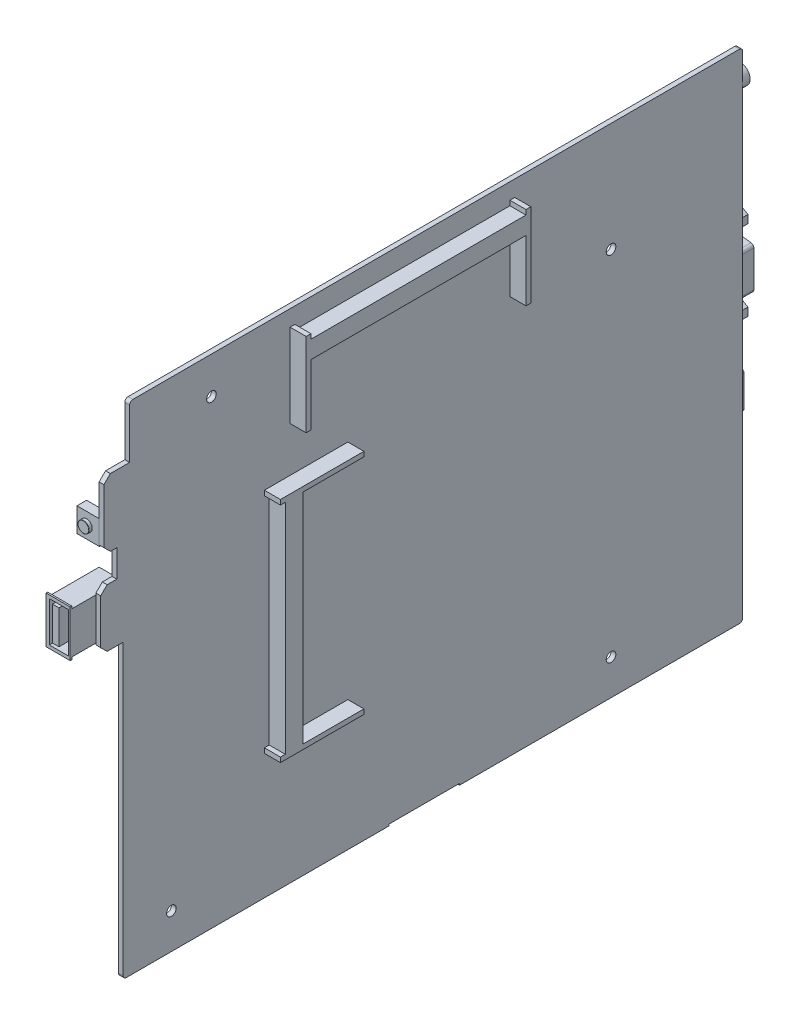
SolidWorks part; units mm, degrees
ref_plane "前视基准面" through (0, 0, 0) normal (0, 0, 1) x (1, 0, 0)
ref_plane "上视基准面" through (0, 0, 0) normal (0, 1, 0) x (1, 0, 0)
ref_plane "右视基准面" through (0, 0, 0) normal (1, 0, 0) x (0, 0, -1)
sketch "草图1" plane through (0, 0, 0) normal (1, 0, 0) x (0, 0, -1)
  line L0 (0, 0) -> (0, 46.6833) construction
  line L1 (-94.5, 77.5) -> (96.5, 77.5)
  line L2 (-96.5, 13.5) -> (-96.5, -77.5)
  line L3 (-96.5, -77.5) -> (96.5, -77.5)
  line L4 (96.5, 77.5) -> (96.5, -77.5)
  line L5 (-94.5, 75.8938) -> (96.5, -77.5) construction
  line L6 (-96.5, -77.5) -> (96.5, 77.5) construction
  line L11 (0, 0) -> (-41.6392, 0) construction
  line L18 (-94.5, 77.5) -> (-94.5, 61)
  line L19 (-94.5, 61) -> (-102.5, 61)
  line L20 (-96.5, 13.5) -> (-103.5, 13.5)
  line L21 (-103.5, 13.5) -> (-103.5, 31.5)
  line L22 (-103.5, 31.5) -> (-98.5, 31.5)
  line L23 (-98.5, 31.5) -> (-98.5, 40)
  line L24 (-98.5, 40) -> (-102.5, 40)
  line L25 (-102.5, 40) -> (-102.5, 61)
  point P0 (0, 0)
  point P21 (-98.5, 35.75)
  dimension "D1" = 193
  dimension "D2" = 155
  dimension "D3" = 8.5
  dimension "D11" = 191
  dimension "D12" = 16.5
  dimension "D13" = 5
  dimension "D14" = 200
  dimension "D15" = 199
  dimension "D16" = 18
  dimension "D17" = 21
extrude "凸台-拉伸1" add sketch "草图1" against normal blind 1.5
chamfer "倒角1" distance 2 angle 45 4 edges at (-0.75, 13.5, 103.5) (-0.75, 31.5, 103.5) (-0.75, 40, 102.5) (-0.75, 61, 102.5)
fillet "圆角1" radius 1 4 edges at (-0.75, 77.5, -96.5) (-0.75, -77.5, -96.5) (-0.75, -77.5, 96.5) (-0.75, 77.5, 94.5)
sketch "草图2" plane through (0, 0, 0) normal (1, 0, 0) x (0, 0, -1)
  line L0 (95.5, 77.5) -> (-93.5, 77.5) construction
  line L1 (-44.5, 72.5) -> (25.5, 72.5)
  line L2 (-44.5, 72.5) -> (-44.5, 35.5)
  line L3 (-44.5, 35.5) -> (25.5, 35.5)
  line L4 (25.5, 72.5) -> (25.5, 35.5)
  line L5 (-52.5, 32.5) -> (-15.5, 32.5)
  line L6 (-52.5, 32.5) -> (-52.5, -38.5)
  line L7 (-52.5, -38.5) -> (-15.5, -38.5)
  line L8 (-15.5, 32.5) -> (-15.5, -38.5)
  line L9 (96.5, -76.5) -> (96.5, 76.5) construction
  line L11 (-85.5, -3.5) -> (-54.5, -3.5)
  line L12 (-85.5, -3.5) -> (-85.5, -60.5)
  line L13 (-85.5, -60.5) -> (-54.5, -60.5)
  line L14 (-54.5, -3.5) -> (-54.5, -60.5)
  dimension "D1" = 70
  dimension "D2" = 71
  dimension "D3" = 37
  dimension "D4" = 37
  dimension "D5" = 45
  dimension "D6" = 5
  dimension "D7" = 71
  dimension "D8" = 112
  dimension "D9" = 31
  dimension "D10" = 57
  dimension "D11" = 2
  dimension "D12" = 81
sketch "草图3" plane through (0, 0, 0) normal (1, 0, 0) x (0, 0, -1)
  line L0 (-44.5, 46.5) -> (-43, 46.5)
  line L1 (-44.5, 72.5) -> (-44.5, 35.5) construction
  line L2 (-43, 46.5) -> (-43, 65.5)
  line L3 (-43, 65.5) -> (24, 65.5)
  line L4 (24, 65.5) -> (24, 46.5)
  line L5 (24, 46.5) -> (25.5, 46.5)
  line L6 (25.5, 72.5) -> (25.5, 35.5) construction
  line L7 (25.5, 46.5) -> (25.5, 72.5)
  line L8 (25.5, 72.5) -> (24, 72.5)
  line L9 (-44.5, 72.5) -> (-44.5, 46.5)
  line L10 (-43, 72.5) -> (-44.5, 72.5)
  line L12 (-43, 72.5) -> (-43, 71)
  line L13 (-43, 71) -> (24, 71)
  line L14 (24, 72.5) -> (24, 71)
  line L15 (-52.5, -38.5) -> (-15.5, -38.5) construction
  line L16 (-52.5, 32.5) -> (-26.5, 32.5)
  line L17 (-52.5, 32.5) -> (-52.5, 31)
  line L18 (-52.5, -38.5) -> (-26.5, -38.5)
  line L19 (-26.5, 32.5) -> (-26.5, 31)
  line L20 (-52.5, -37) -> (-52.5, -38.5)
  line L21 (-26.5, -37) -> (-45.5, -37)
  line L23 (-26.5, 31) -> (-45.5, 31)
  line L24 (-45.5, -37) -> (-45.5, 31)
  line L25 (-52.5, 31) -> (-51, 31)
  line L27 (-52.5, -37) -> (-51, -37)
  line L28 (-51, 31) -> (-51, -37)
  line L29 (-26.5, -37) -> (-26.5, -38.5)
  dimension "D1" = 1.5
  dimension "D2" = 7
  dimension "D3" = 5.5
  dimension "D4" = 26
  dimension "D5" = 5.5
  dimension "D6" = 7
extrude "凸台-拉伸2" add sketch "草图3" along normal blind 5
sketch "草图4" plane through (-1.5, 0, 0) normal (-1, 0, 0) x (0, 0, 1)
  line L0 (95.5, -77.5) -> (-95.5, -77.5) construction
  line L1 (-9.75, -70) -> (15.25, -70)
  line L2 (-9.75, -70) -> (-9.75, -78.5)
  line L3 (-9.75, -78.5) -> (15.25, -78.5)
  line L4 (15.25, -70) -> (15.25, -78.5)
  line L6 (-96.5, -76.5) -> (-96.5, 76.5) construction
  dimension "D1" = 8.5
  dimension "D2" = 25
  dimension "D3" = 7.5
  dimension "D4" = 111.75
extrude "凸台-拉伸3" add sketch "草图4" along normal blind 11
sketch "草图5" plane through (-12.5, 0, 0) normal (-1, 0, 0) x (0, 0, 1)
  line L0 (-9.75, -70) -> (-9.75, -78.5) construction
  line L1 (-8.25, -72.5) -> (3.25, -72.5)
  line L2 (-8.25, -72.5) -> (-8.25, -74.5)
  line L3 (-8.25, -74.5) -> (3.25, -74.5)
  line L4 (3.25, -72.5) -> (3.25, -74.5)
  line L5 (4.75, -72.5) -> (13.75, -72.5)
  line L6 (4.75, -72.5) -> (4.75, -74.5)
  line L7 (4.75, -74.5) -> (13.75, -74.5)
  line L8 (13.75, -72.5) -> (13.75, -74.5)
  line L9 (-9.75, -72.5) -> (-9.25, -72.5)
  line L10 (-9.75, -72.5) -> (-9.75, -74.5)
  line L11 (-9.75, -74.5) -> (-9.25, -74.5)
  line L12 (-9.25, -72.5) -> (-9.25, -74.5)
  line L13 (15.25, -78.5) -> (15.25, -70) construction
  line L14 (15.25, -72.5) -> (14.75, -72.5)
  line L15 (15.25, -72.5) -> (15.25, -74.5)
  line L16 (15.25, -74.5) -> (14.75, -74.5)
  line L17 (14.75, -72.5) -> (14.75, -74.5)
  line L18 (15.25, -70) -> (-9.75, -70) construction
  dimension "D1" = 0.5
  dimension "D2" = 2.5
  dimension "D3" = 2
  dimension "D4" = 1
  dimension "D5" = 1.5
  dimension "D6" = 1
  dimension "D7" = 11.5
extrude "切除-拉伸1" cut sketch "草图5" against normal blind 8
sketch "草图6" plane through (-12.5, 0, 0) normal (-1, 0, 0) x (0, 0, 1)
  line L0 (-9.75, -78.5) -> (15.25, -78.5) construction
  line L1 (-8.25, -78.5) -> (13.75, -78.5)
  line L2 (-8.25, -78.5) -> (-8.25, -77)
  line L3 (-8.25, -77) -> (13.75, -77)
  line L4 (13.75, -78.5) -> (13.75, -77)
  line L5 (4.75, -74.5) -> (13.75, -74.5) construction
  line L6 (-8.25, -72.5) -> (-8.25, -74.5) construction
  line L7 (13.75, -74.5) -> (13.75, -72.5) construction
  dimension "D1" = 2.5
extrude "切除-拉伸2" cut sketch "草图6" against normal through all
sketch "草图7" plane through (-1.5, 0, 0) normal (-1, 0, 0) x (0, 0, 1)
  line L0 (103.5, 22.5) -> (89.2944, 22.5) construction
  line L1 (111, 29.75) -> (111.5, 29.75)
  line L2 (95.5, 29) -> (95.5, 16)
  line L3 (111, 15.25) -> (111.5, 15.25)
  line L4 (111.5, 29.75) -> (111.5, 15.25)
  line L6 (103.5, 29.5) -> (103.5, 15.5) construction
  line L10 (95.5, 29) -> (111, 29)
  line L11 (111, 29.75) -> (111, 29)
  line L14 (95.5, 16) -> (111, 16)
  line L15 (111, 15.25) -> (111, 16)
  dimension "D1" = 0.5
  dimension "D2" = 14.5
  dimension "D3" = 16
  dimension "D4" = 8
  dimension "D5" = 13
extrude "凸台-拉伸4" add sketch "草图7" along normal blind 7.5
sketch "草图8" plane through (-9, 0, 0) normal (-1, 0, 0) x (0, 0, 1)
  line L1 (95.5, 29) -> (111, 29)
  line L2 (95.5, 29) -> (95.5, 16)
  line L3 (95.5, 16) -> (111, 16)
  line L4 (111, 29) -> (111, 16)
extrude "切除-拉伸3" cut sketch "草图8" against normal blind 0.5
sketch "草图9" plane through (0, 0, 111.5) normal (0, 0, 1) x (1, 0, 0)
  line L0 (-9, 29.75) -> (-1.5, 29.75) construction
  line L1 (-8, 28.75) -> (-2, 28.75)
  line L2 (-8, 28.75) -> (-8, 16.25)
  line L3 (-8, 16.25) -> (-2, 16.25)
  line L4 (-2, 28.75) -> (-2, 16.25)
  line L5 (-7, 27.75) -> (-5, 27.75)
  line L6 (-7, 27.75) -> (-7, 17.25)
  line L7 (-7, 17.25) -> (-5, 17.25)
  line L8 (-5, 27.75) -> (-5, 17.25)
  line L9 (-9, 15.25) -> (-9, 29.75) construction
  line L10 (-9, 15.25) -> (-1.5, 15.25) construction
  line L11 (-1.5, 29) -> (-1.5, 16) construction
  dimension "D1" = 1
  dimension "D2" = 1
  dimension "D3" = 1
  dimension "D4" = 0.5
  dimension "D5" = 1
  dimension "D6" = 2
  dimension "D7" = 1
  dimension "D8" = 1
extrude "切除-拉伸4" cut sketch "草图9" against normal blind 13
sketch "草图10" plane through (-1.5, 0, 0) normal (-1, 0, 0) x (0, 0, 1)
  line L0 (102.5, 59) -> (102.5, 42) construction
  line L1 (102.4, 49) -> (99.4, 49)
  line L3 (102.4, 41.5) -> (99.4, 41.5)
  line L4 (99.4, 49) -> (99.4, 41.5)
  line L5 (94.5, 61) -> (100.5, 61) construction
  line L6 (102.4, 49) -> (102.4, 41.5)
  dimension "D1" = 12
  dimension "D2" = 7.5
  dimension "D3" = 3
  dimension "D4" = 0.1
extrude "凸台-拉伸5" add sketch "草图10" along normal blind 7
sketch "草图11" plane through (0, 0, 102.4) normal (0, 0, 1) x (1, 0, 0)
  line L0 (-8.5, 45.25) -> (1.2672, 45.25) construction
  line L1 (-8.5, 41.5) -> (-8.5, 49) construction
  circle A0 centre (-5.5, 45.25) radius 1.75
  dimension "D1" = 3.5
  dimension "D2" = 3
extrude "凸台-拉伸6" add sketch "草图11" along normal blind 1
fillet "圆角2" radius 0.1 1 edges at (-3.75, 45.25, 103.4)
sketch "草图12" plane through (-1.5, 0, 0) normal (-1, 0, 0) x (0, 0, 1)
  line L0 (-96.5, -76.5) -> (-96.5, 76.5) construction
  line L1 (-96.6, 72.5) -> (-81.6, 72.5)
  line L2 (-96.6, 72.5) -> (-96.6, 62.5)
  line L3 (-96.6, 62.5) -> (-81.6, 62.5)
  line L4 (-81.6, 72.5) -> (-81.6, 62.5)
  line L5 (-95.5, 77.5) -> (93.5, 77.5) construction
  dimension "D1" = 0.1
  dimension "D2" = 5
  dimension "D3" = 15
  dimension "D4" = 10
extrude "凸台-拉伸7" add sketch "草图12" along normal blind 4.5
sketch "草图13" plane through (0, 0, -96.6) normal (0, 0, -1) x (-1, 0, 0)
  line L0 (6, 67.5) -> (9.0348, 67.5) construction
  line L1 (6, 72.5) -> (6, 62.5) construction
  line L5 (0, -76.5) -> (0, 76.5) construction
  circle A0 centre (3.25, 67.5) radius 3
  circle A1 centre (3.25, 67.5) radius 1.5
  point P9 (0, 0)
  dimension "D1" = 6
  dimension "D2" = 3
  dimension "D3" = 3.25
extrude "凸台-拉伸8" add sketch "草图13" along normal blind 2.5
sketch "草图14" plane through (-1.5, 0, 0) normal (-1, 0, 0) x (0, 0, 1)
  line L0 (-96.5, -76.5) -> (-96.5, 62.5) construction
  line L1 (-96.4, 60.5) -> (-93.9, 60.5)
  line L2 (-96.4, 60.5) -> (-96.4, 53.5)
  line L3 (-96.4, 53.5) -> (-93.9, 53.5)
  line L4 (-93.9, 60.5) -> (-93.9, 53.5)
  line L5 (-96.4, 50.5) -> (-93.9, 50.5)
  line L6 (-96.4, 50.5) -> (-96.4, 43.5)
  line L7 (-96.4, 43.5) -> (-93.9, 43.5)
  line L8 (-93.9, 50.5) -> (-93.9, 43.5)
  line L9 (-96.5, 62.5) -> (-81.6, 62.5) construction
  dimension "D1" = 0.1
  dimension "D2" = 7
  dimension "D3" = 2.5
  dimension "D4" = 2
  dimension "D5" = 3
extrude "凸台-拉伸9" add sketch "草图14" along normal blind 3.5
sketch "草图15" plane through (0, 0, -96.4) normal (0, 0, -1) x (-1, 0, 0)
  line L0 (5, 57) -> (1.1058, 57) construction
  line L1 (2.5, 58.5) -> (4, 58.5)
  line L2 (2.5, 58.5) -> (2.5, 55.5)
  line L3 (2.5, 55.5) -> (4, 55.5)
  line L4 (4, 58.5) -> (4, 55.5)
  line L5 (5, 60.5) -> (5, 53.5) construction
  line L6 (3.25, 60.5) -> (3.25, 53.0774) construction
  line L7 (5, 60.5) -> (1.5, 60.5) construction
  line L8 (5, 47) -> (-0.6417, 47) construction
  line L9 (5, 50.5) -> (5, 43.5) construction
  line L11 (2.5, 48.5) -> (4, 48.5)
  line L12 (2.5, 48.5) -> (2.5, 45.5)
  line L13 (2.5, 45.5) -> (4, 45.5)
  line L14 (4, 48.5) -> (4, 45.5)
  dimension "D1" = 1.5
  dimension "D2" = 3
extrude "凸台-拉伸10" add sketch "草图15" along normal blind 1
sketch "草图16" plane through (-1.5, 0, 0) normal (-1, 0, 0) x (0, 0, 1)
  line L0 (-96.5, -76.5) -> (-96.5, 62.5) construction
  line L1 (-95.5, 41.5) -> (-92.5, 41.5)
  line L2 (-95.5, 41.5) -> (-95.5, 32.5)
  line L3 (-95.5, 32.5) -> (-92.5, 32.5)
  line L4 (-92.5, 41.5) -> (-92.5, 32.5)
  line L5 (-96.4, 43.5) -> (-93.9, 43.5) construction
  dimension "D1" = 1
  dimension "D2" = 9
  dimension "D3" = 3
  dimension "D4" = 2
extrude "凸台-拉伸11" add sketch "草图16" along normal blind 2.5
sketch "草图17" plane through (0, 0, -95.5) normal (0, 0, -1) x (-1, 0, 0)
  line L0 (4, 41.5) -> (4, 32.5) construction
  line L1 (2.5, 40) -> (3, 40)
  line L2 (2.5, 40) -> (2.5, 38.5)
  line L3 (2.5, 38.5) -> (3, 38.5)
  line L4 (3, 40) -> (3, 38.5)
  line L5 (4, 41.5) -> (1.5, 41.5) construction
  dimension "D1" = 0.5
  dimension "D2" = 1.5
  dimension "D3" = 1
  dimension "D4" = 1.5
extrude "凸台-拉伸12" add sketch "草图17" along normal blind 2
sketch "草图18" plane through (-1.5, 0, 0) normal (-1, 0, 0) x (0, 0, 1)
  line L0 (-96.5, -76.5) -> (-96.5, 62.5) construction
  line L1 (-97.5, 28) -> (-93, 28)
  line L2 (-97.5, 28) -> (-97.5, -3)
  line L3 (-97.5, -3) -> (-93, -3)
  line L4 (-93, 28) -> (-93, -3)
  line L5 (-95.5, 32.5) -> (-92.5, 32.5) construction
  point P6 (-95.25, 28)
  dimension "D1" = 1
  dimension "D2" = 4.5
  dimension "D3" = 4.5
  dimension "D4" = 31
extrude "凸台-拉伸13" add sketch "草图18" along normal blind 12
sketch "草图19" plane through (0, 0, -97.5) normal (0, 0, -1) x (-1, 0, 0)
  line L0 (7.5, 28) -> (7.5, 8.154) construction
  line L1 (7.5, 22.5) -> (9.6651, 23.75)
  line L2 (9.6651, 23.75) -> (9.6651, 26.25)
  line L3 (9.6651, 26.25) -> (7.5, 27.5)
  line L4 (7.5, 27.5) -> (5.3349, 26.25)
  line L5 (5.3349, 26.25) -> (5.3349, 23.75)
  line L6 (5.3349, 23.75) -> (7.5, 22.5)
  line L7 (7.5, -2.5) -> (9.6651, -1.25)
  line L8 (9.6651, -1.25) -> (9.6651, 1.25)
  line L9 (9.6651, 1.25) -> (7.5, 2.5)
  line L10 (7.5, 2.5) -> (5.3349, 1.25)
  line L11 (5.3349, 1.25) -> (5.3349, -1.25)
  line L12 (5.3349, -1.25) -> (7.5, -2.5)
  line L13 (13.5, 28) -> (1.5, 28) construction
  line L14 (13.5, 12.5) -> (1.5, 12.5) construction
  line L15 (13.5, 28) -> (13.5, -3) construction
  line L16 (1.5, 28) -> (1.5, -3) construction
  circle A0 centre (7.5, 25) radius 2.1651 construction
  circle A1 centre (7.5, 0) radius 2.1651 construction
  dimension "D1" = 2.5
  dimension "D2" = 25
extrude "凸台-拉伸14" add sketch "草图19" along normal blind 6
sketch "草图20" plane through (0, 0, -97.5) normal (0, 0, -1) x (-1, 0, 0)
  line L0 (3.5, 18.1172) -> (3.5, 6.8828)
  line L1 (4.376, 5.8905) -> (10.376, 5.1405)
  line L2 (11.5, 6.1328) -> (11.5, 18.8672)
  line L3 (10.376, 19.8595) -> (4.376, 19.1095)
  line L4 (13.5, 12.5) -> (-2.3142, 12.5) construction
  line L5 (13.5, 28) -> (13.5, -3) construction
  line L6 (7.5, 28) -> (7.5, -3) construction
  line L7 (13.5, 28) -> (1.5, 28) construction
  line L8 (13.5, -3) -> (1.5, -3) construction
  arc A0 (4.376, 5.8905) -> (3.5, 6.8828) centre (4.5, 6.8828) cw
  arc A1 (3.5, 18.1172) -> (4.376, 19.1095) centre (4.5, 18.1172) cw
  arc A2 (10.376, 5.1405) -> (11.5, 6.1328) centre (10.5, 6.1328) ccw
  arc A3 (11.5, 18.8672) -> (10.376, 19.8595) centre (10.5, 18.8672) ccw
  point P16 (3.5, 6)
  point P19 (3.5, 19)
  point P22 (11.5, 5)
  point P25 (11.5, 20)
  dimension "D4" = 1
  dimension "D5" = 1
  dimension "D1" = 8
  dimension "D2" = 13
  dimension "D3" = 15
extrude "凸台-拉伸15" add sketch "草图20" along normal up to surface (6 mm away) up to face at (-7.5, 0, -103.5)
hole_wizard "M3 螺纹孔1" positions "草图21" profile "草图22" tap size "M3" standard "GB"
sketch "草图21" plane through (0, 0, -103.5) normal (0, 0, -1) x (-1, 0, 0)
  point P0 (7.5079, 25.0935)
  point P3 (7.5079, 0)
sketch "草图22" plane through (-7.5079, 25.0935, -103.5) normal (1, 0, 0) x (0, 1, 0)
  line L0 (0, 0) -> (0, 8.2511)
  line L1 (0, 8.2511) -> (1.25, 7.5)
  line L2 (1.25, 7.5) -> (1.25, 0.25)
  line L3 (1.25, 0.25) -> (1.5, 0)
  line L5 (1.5, 0) -> (0, 0)
  line L6 (-1.25, 0.25) -> (-1.5, 0) construction
  line L10 (0, 8.2511) -> (-1.25, 7.5) construction
  line L11 (0, -6.35) -> (0, 107.95) construction
  dimension "螺纹孔钻头直径" = 2.5
  dimension "螺纹孔钻头深度" = 7.5
  dimension "近端锥形沉头孔直径" = 3
  dimension "近端锥形沉头孔角度" = 90
  dimension "导头角度" = 118
cosmetic thread "孔螺蚊线1" parameters "D1"=6, "D2"=3
cosmetic thread "孔螺蚊线2" parameters "D1"=6, "D2"=3
sketch "草图23" plane through (0, 0, -103.5) normal (0, 0, -1) x (-1, 0, 0)
  line L0 (7.376, 19.4845) -> (7.376, 11.5981) construction
  line L1 (10.376, 19.8595) -> (4.376, 19.1095) construction
  line L2 (9.5, 17.5) -> (7.7703, 17.5) construction
  line L3 (11.5, 6.1328) -> (11.5, 18.8672) construction
  line L4 (3.5, 18.1172) -> (3.5, 6.8828) construction
  line L5 (11.5, 12.5) -> (3.5, 12.5) construction
  line L6 (11.5, 6.1328) -> (11.5, 18.8672) construction
  line L7 (3.5, 18.1172) -> (3.5, 6.8828) construction
  circle A0 centre (9.5, 17.5) radius 0.5
  circle A1 centre (7.376, 16.25) radius 0.5
  circle A2 centre (5.5, 17.5) radius 0.5
  dimension "D1" = 1
  dimension "D2" = 2
  dimension "D3" = 2
  dimension "D4" = 10
  dimension "D5" = 1.25
extrude "切除-拉伸5" cut sketch "草图23" against normal blind 5
pattern_linear "阵列(线性)1" count 5 spacing 2.5 along (0, -1, 0) of "切除-拉伸5"
sketch "草图24" plane through (-1.5, 0, 0) normal (-1, 0, 0) x (0, 0, 1)
  line L0 (-96.5, -76.5) -> (-96.5, -3) construction
  line L1 (-98.5, -9.5) -> (-86.5, -9.5)
  line L2 (-98.5, -9.5) -> (-98.5, -24.5)
  line L3 (-98.5, -24.5) -> (-86.5, -24.5)
  line L4 (-86.5, -9.5) -> (-86.5, -24.5)
  line L5 (-96.5, -3) -> (-93, -3) construction
  dimension "D1" = 2
  dimension "D2" = 6.5
  dimension "D3" = 12
  dimension "D4" = 15
extrude "凸台-拉伸16" add sketch "草图24" along normal blind 6
sketch "草图25" plane through (0, 0, -98.5) normal (0, 0, -1) x (-1, 0, 0)
  line L0 (7.5, -9.5) -> (1.5, -9.5) construction
  line L1 (1.5, -9.5) -> (3.5, -9.5)
  line L2 (3.5, -9.5) -> (1.5, -12)
  line L3 (1.5, -9.5) -> (1.5, -24.5) construction
  line L4 (1.5, -12) -> (1.5, -9.5)
  line L5 (1.5, -22) -> (3.5, -24.5)
  line L6 (1.5, -24.5) -> (1.5, -9.5) construction
  line L7 (7.5, -24.5) -> (1.5, -24.5) construction
  line L8 (3.5, -24.5) -> (1.5, -24.5)
  line L9 (1.5, -24.5) -> (1.5, -22)
  line L10 (7.5, -9.5) -> (7.5, -24.5) construction
  line L11 (7.5, -17) -> (1.5, -17) construction
  line L12 (7, -10) -> (3.7403, -10)
  line L13 (3.7403, -10) -> (2, -12.1754)
  line L14 (2, -12.1754) -> (2, -21.8246)
  line L15 (2, -21.8246) -> (3.7403, -24)
  line L16 (3.7403, -24) -> (7, -24)
  line L17 (7, -24) -> (7, -10)
  line L19 (4, -12) -> (5, -12)
  line L20 (4, -12) -> (4, -22)
  line L21 (4, -22) -> (5, -22)
  line L22 (5, -12) -> (5, -22)
  dimension "D1" = 4
  dimension "D2" = 10
  dimension "D3" = 0.5
  dimension "D4" = 0.5
  dimension "D5" = 0.5
  dimension "D6" = 0.5
  dimension "D7" = 0.5
  dimension "D8" = 0.5
  dimension "D9" = 1
  dimension "D10" = 2
  dimension "D11" = 2
extrude "切除-拉伸6" cut sketch "草图25" against normal blind 10
sketch "草图26" plane through (0, 0, -98.5) normal (0, 0, -1) x (-1, 0, 0)
  line L1 (4, -12) -> (5, -12)
  line L2 (4, -12) -> (4, -22)
  line L3 (4, -22) -> (5, -22)
  line L4 (5, -12) -> (5, -22)
extrude "切除-拉伸7" cut sketch "草图26" against normal blind 2
sketch "草图27" plane through (-1.5, 0, 0) normal (-1, 0, 0) x (0, 0, 1)
  line L0 (-96.5, -76.5) -> (-96.5, -22) construction
  line L1 (-98, -28) -> (-69.5, -28)
  line L2 (-98, -28) -> (-98, -45.5)
  line L3 (-98, -45.5) -> (-69.5, -45.5)
  line L4 (-69.5, -28) -> (-69.5, -45.5)
  line L5 (-98.5, -24.5) -> (-86.5, -24.5) construction
  dimension "D1" = 1.5
  dimension "D2" = 28.5
  dimension "D3" = 17.5
  dimension "D4" = 3.5
extrude "凸台-拉伸17" add sketch "草图27" along normal blind 26
sketch "草图28" plane through (0, 0, -98) normal (0, 0, -1) x (-1, 0, 0)
  line L0 (27.5, -36.75) -> (26, -36.75) construction
  line L1 (4.5, -30.75) -> (11.5, -30.75)
  line L2 (4.5, -30.75) -> (4.5, -33.75)
  line L3 (4.5, -42.75) -> (11.5, -42.75)
  line L4 (11.5, -30.75) -> (11.5, -42.75)
  line L5 (27.5, -28) -> (27.5, -45.5) construction
  line L6 (1.5, -45.5) -> (1.5, -28) construction
  line L7 (4.5, -39.75) -> (4.5, -42.75)
  line L8 (4.5, -33.75) -> (3, -33.75)
  line L10 (4.5, -39.75) -> (3, -39.75)
  line L11 (3, -33.75) -> (3, -39.75)
  line L12 (1.5, -28) -> (1.5, -45.5) construction
  line L13 (24.5, -39.75) -> (24.5, -42.75)
  line L14 (17.5, -30.75) -> (24.5, -30.75)
  line L15 (17.5, -30.75) -> (17.5, -42.75)
  line L16 (17.5, -42.75) -> (24.5, -42.75)
  line L17 (24.5, -30.75) -> (24.5, -33.75)
  line L18 (24.5, -33.75) -> (26, -33.75)
  line L20 (24.5, -39.75) -> (26, -39.75)
  line L21 (26, -33.75) -> (26, -39.75)
  line L22 (21.5667, -36.75) -> (1.5, -36.75) construction
  point P14 (4.5, -32.25)
  dimension "D1" = 6
  dimension "D2" = 12
  dimension "D3" = 7
  dimension "D4" = 1.5
  dimension "D5" = 1.5
  dimension "D6" = 1.5
extrude "切除-拉伸8" cut sketch "草图28" against normal blind 10
sketch "草图29" plane through (0, 0, -98) normal (0, 0, -1) x (-1, 0, 0)
  line L0 (26, -39.75) -> (26, -33.75) construction
  line L1 (26, -34.75) -> (27.5, -34.75)
  line L2 (26, -34.75) -> (26, -38.75)
  line L3 (26, -38.75) -> (27.5, -38.75)
  line L4 (27.5, -34.75) -> (27.5, -38.75)
  line L5 (27.5, -28) -> (27.5, -45.5) construction
  line L6 (1.5, -36.75) -> (29.6783, -36.75) construction
  line L7 (1.5, -45.5) -> (1.5, -28) construction
  line L8 (1.5, -28) -> (1.5, -45.5) construction
  line L9 (1.5, -34.75) -> (3, -34.75)
  line L10 (1.5, -34.75) -> (1.5, -38.75)
  line L11 (1.5, -38.75) -> (3, -38.75)
  line L12 (3, -34.75) -> (3, -38.75)
  line L13 (3, -33.75) -> (3, -39.75) construction
  dimension "D1" = 4
extrude "切除-拉伸9" cut sketch "草图29" against normal blind 3
sketch "草图30" plane through (-1.5, 0, 0) normal (-1, 0, 0) x (0, 0, 1)
  line L0 (-96.5, -45.5) -> (-69.5, -45.5) construction
  line L1 (-97.5, -48) -> (-97, -48)
  line L2 (-97.5, -48) -> (-97.5, -63)
  line L3 (-97.5, -63) -> (-97, -63)
  line L4 (-80.5, -49) -> (-80.5, -62)
  line L5 (-97.5, -55.5) -> (-73.7235, -55.5) construction
  line L6 (-96.5, -76.5) -> (-96.5, -45.5) construction
  line L9 (-80.5, -49) -> (-97, -49)
  line L13 (-80.5, -62) -> (-97, -62)
  line L14 (-97, -63) -> (-97, -62)
  line L15 (-97, -49) -> (-97, -48)
  dimension "D1" = 2.5
  dimension "D2" = 15
  dimension "D3" = 13
  dimension "D4" = 1
  dimension "D5" = 0.5
  dimension "D6" = 17
extrude "凸台-拉伸18" add sketch "草图30" along normal blind 15
sketch "草图31" plane through (-16.5, 0, 0) normal (-1, 0, 0) x (0, 0, 1)
  line L1 (-80.5, -49) -> (-97, -49)
  line L2 (-80.5, -49) -> (-80.5, -62)
  line L3 (-80.5, -62) -> (-97, -62)
  line L4 (-97, -49) -> (-97, -62)
extrude "切除-拉伸10" cut sketch "草图31" against normal blind 0.5
sketch "草图32" plane through (0, 0, -97.5) normal (0, 0, -1) x (-1, 0, 0)
  line L0 (1.5, -55.5) -> (16.5, -55.5) construction
  line L1 (10.5, -49.5) -> (15.5, -49.5)
  line L2 (10.5, -49.5) -> (10.5, -61.5)
  line L3 (10.5, -61.5) -> (15.5, -61.5)
  line L4 (15.5, -49.5) -> (15.5, -61.5)
  line L5 (1.5, -48) -> (1.5, -63) construction
  line L6 (16.5, -48) -> (16.5, -63) construction
  line L7 (16.5, -48) -> (1.5, -48) construction
  line L8 (12.5, -51) -> (14, -51)
  line L9 (12.5, -51) -> (12.5, -60)
  line L10 (12.5, -60) -> (14, -60)
  line L11 (14, -51) -> (14, -60)
  line L12 (2.5, -49.5) -> (7.5, -49.5)
  line L13 (2.5, -49.5) -> (2.5, -61.5)
  line L14 (2.5, -61.5) -> (7.5, -61.5)
  line L15 (7.5, -49.5) -> (7.5, -61.5)
  line L16 (6, -51) -> (4.5, -51)
  line L17 (6, -51) -> (6, -60)
  line L18 (6, -60) -> (4.5, -60)
  line L19 (4.5, -51) -> (4.5, -60)
  dimension "D1" = 5
  dimension "D2" = 1
  dimension "D3" = 1.5
  dimension "D4" = 1.5
  dimension "D5" = 1.5
  dimension "D6" = 3
  dimension "D7" = 1.5
  dimension "D8" = 1.5
extrude "切除-拉伸11" cut sketch "草图32" against normal blind 10
sketch "草图33" plane through (-1.5, 0, 0) normal (-1, 0, 0) x (0, 0, 1)
  line L0 (-9.75, -77.5) -> (-95.5, -77.5) construction
  line L1 (-98, -66.5) -> (-85, -66.5)
  line L2 (-98, -66.5) -> (-98, -76.5)
  line L3 (-98, -76.5) -> (-85, -76.5)
  line L4 (-85, -66.5) -> (-85, -76.5)
  line L6 (-96.5, -76.5) -> (-96.5, -62) construction
  dimension "D1" = 1
  dimension "D2" = 10
  dimension "D3" = 13
  dimension "D4" = 1.5
extrude "凸台-拉伸19" add sketch "草图33" along normal blind 10
sketch "草图34" plane through (0, 0, -98) normal (0, 0, -1) x (-1, 0, 0)
  line L0 (11.5, -71.5) -> (1.5, -71.5) construction
  line L1 (11.5, -66.5) -> (11.5, -76.5) construction
  line L2 (1.5, -66.5) -> (1.5, -76.5) construction
  line L3 (6.5, -66.5) -> (6.5, -76.5) construction
  line L4 (11.5, -66.5) -> (1.5, -66.5) construction
  line L5 (11.5, -76.5) -> (1.5, -76.5) construction
  circle A0 centre (6.5, -71.5) radius 3
  circle A1 centre (6.5, -71.5) radius 0.75
  dimension "D1" = 6
  dimension "D2" = 1.5
extrude "切除-拉伸12" cut sketch "草图34" against normal blind 10
sketch "草图35" plane through (0, 0, -98) normal (0, 0, -1) x (-1, 0, 0)
  circle A0 centre (6.5, -71.5) radius 0.75
extrude "切除-拉伸13" cut sketch "草图35" against normal blind 2
fillet "圆角3" radius 0.75 1 edges at (-7.25, -71.5, -96)
sketch "草图36" plane through (0, 0, 0) normal (1, 0, 0) x (0, 0, -1)
  line L0 (-81.5, -66.5) -> (-11.0225, -66.5) construction
  line L1 (96.5, -76.5) -> (96.5, 76.5) construction
  line L2 (55.5, -66.5) -> (55.5, -26.1572) construction
  line L3 (-95.5, -77.5) -> (-13.75, -77.5) construction
  circle A0 centre (-69, 66) radius 1.5
  circle A1 centre (-81.5, -66.5) radius 1.5
  circle A2 centre (55.5, -66.5) radius 1.5
  circle A3 centre (55.5, 43.5) radius 1.5
  dimension "D1" = 137
  dimension "D5" = 3
  dimension "D2" = 110
  dimension "D3" = 41
  dimension "D4" = 11
  dimension "D6" = 124.5
  dimension "D7" = 132.5
extrude "切除-拉伸14" cut sketch "草图36" against normal blind 10
sketch "草图37" plane through (0, 0, -97.4) normal (0, 0, -1) x (-1, 0, 0)
  line L0 (3.2779, 58.9413) -> (3.2779, 78.464) construction
